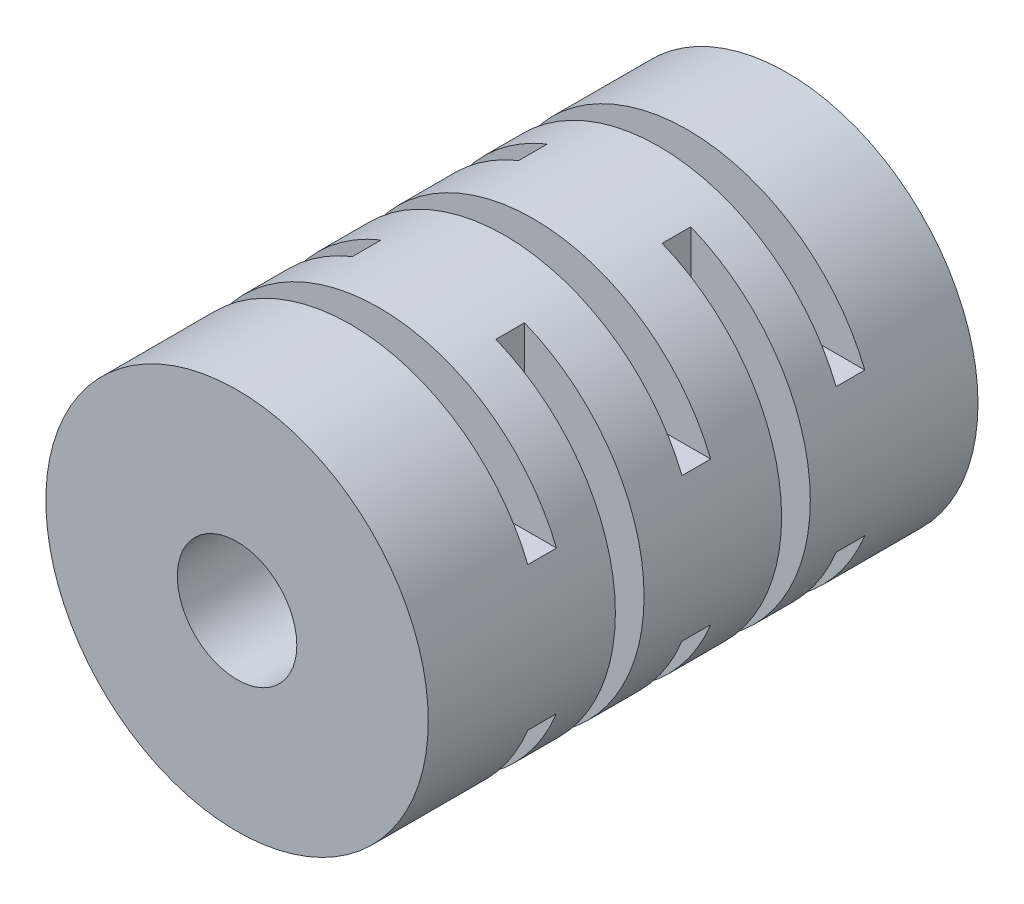
SolidWorks part; units mm, degrees
ref_plane "Front Plane" through (0, 0, 0) normal (0, 0, 1) x (1, 0, 0)
ref_plane "Top Plane" through (0, 0, 0) normal (0, 1, 0) x (1, 0, 0)
ref_plane "Right Plane" through (0, 0, 0) normal (1, 0, 0) x (0, 0, -1)
sketch "Sketch1" plane through (0, 0, 0) normal (0, 0, 1) x (1, 0, 0)
  circle A0 centre (0, 0) radius 2.5
  circle A1 centre (0, 0) radius 8
  dimension "D1" = 5
  dimension "D2" = 16
extrude "Boss-Extrude1" add sketch "Sketch1" along normal blind 23
sketch "Sketch2" plane through (0, 0, 0) normal (0, 1, 0) x (1, 0, 0)
  line L1 (-15.1369, -7.0167) -> (-3, -7.0167)
  line L2 (-15.1369, -7.0167) -> (-15.1369, -8.2167)
  line L3 (-15.1369, -8.2167) -> (-3, -8.2167)
  line L4 (-3, -7.0167) -> (-3, -8.2167)
  line L5 (-14.7546, -13.9712) -> (-3, -13.9712)
  line L6 (-14.7546, -13.9712) -> (-14.7546, -15.1712)
  line L7 (-14.7546, -15.1712) -> (-3, -15.1712)
  line L8 (-3, -13.9712) -> (-3, -15.1712)
  dimension "D1" = 3
  dimension "D2" = 1.2
extrude "Cut-Extrude1" cut sketch "Sketch2" against normal through all and the other way through all
pattern_circular "CirPattern1" count 2 over 360 about axis through (0, 0, 23) along (0, 0, -1) of "Cut-Extrude1"
sketch "Sketch3" plane through (0, 0, 0) normal (1, 0, 0) x (0, 0, -1)
  line L0 (-15.1712, 7.4162) -> (-13.9712, 7.4162) construction
  line L1 (-11.8011, 11.3693) -> (-10.6011, 11.3693)
  line L2 (-11.8011, 11.3693) -> (-11.8011, 3)
  line L3 (-11.8011, 3) -> (-10.6011, 3)
  line L4 (-10.6011, 11.3693) -> (-10.6011, 3)
  line L5 (-18.251, 11.3385) -> (-17.051, 11.3385)
  line L6 (-18.251, 11.3385) -> (-18.251, 3)
  line L7 (-18.251, 3) -> (-17.051, 3)
  line L8 (-17.051, 11.3385) -> (-17.051, 3)
  line L9 (-5.3512, 10.9693) -> (-4.1512, 10.9693)
  line L10 (-5.3512, 10.9693) -> (-5.3512, 3)
  line L11 (-5.3512, 3) -> (-4.1512, 3)
  line L12 (-4.1512, 10.9693) -> (-4.1512, 3)
  dimension "D1" = 3
extrude "Cut-Extrude2" cut sketch "Sketch3" against normal through all and the other way through all
pattern_circular "CirPattern2" count 2 over 360 about axis through (0, 0, 23) along (0, 0, -1) of "Cut-Extrude2"
